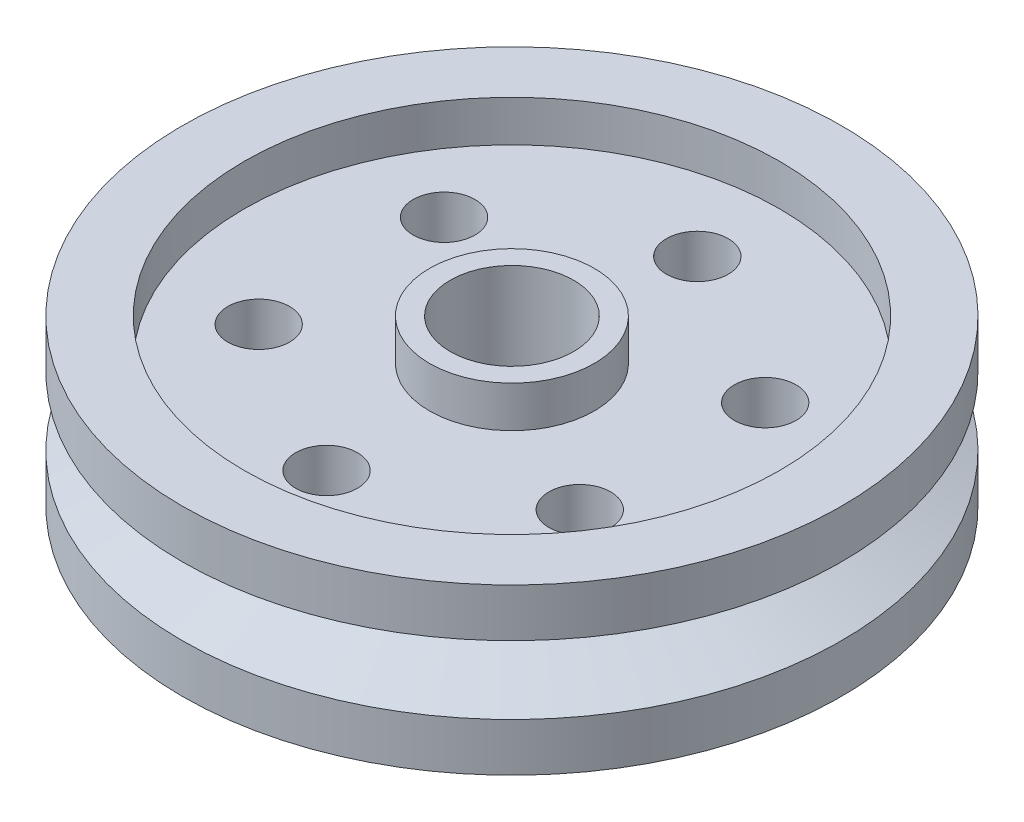
SolidWorks part; units mm, degrees
material "Aluminum Bronze"
ref_plane "Front" through (0, 0, 0) normal (0, 0, 1) x (1, 0, 0)
ref_plane "Top" through (0, 0, 0) normal (0, 1, 0) x (1, 0, 0)
ref_plane "Right" through (0, 0, 0) normal (1, 0, 0) x (0, 0, -1)
sketch "Sketch1" plane through (0, 0, 0) normal (0, 0, 1) x (1, 0, 0)
  line L0 (0, 218.8321) -> (0, -193.7631) construction
  line L1 (-236.0671, 0) -> (246.5126, 0) construction
  line L2 (0, 0) -> (0, 12.7)
  line L3 (0, 12.7) -> (50.8, 12.7)
  line L4 (50.8, 12.7) -> (50.8, 5.2605)
  line L5 (50.8, 5.2605) -> (38.1, 0)
  line L6 (38.1, 0) -> (0, 0)
  dimension "D1" = 101.6
  dimension "D2" = 12.7
  dimension "D3" = 22.5
  dimension "D4" = 25.4
revolve "Revolve1" add sketch "Sketch1" angle 360 about L0
sketch "Sketch2" plane through (0, 12.7, 0) normal (0, 1, 0) x (1, 0, 0)
  circle A0 centre (0, 0) radius 41.275
  circle A1 centre (0, 0) radius 12.7
  dimension "D1" = 82.55
  dimension "D2" = 25.4
extrude "Cut-Extrude1" cut sketch "Sketch2" against normal blind 6.35
sketch "Sketch3" plane through (0, 12.7, 0) normal (0, 1, 0) x (1, 0, 0)
  circle A0 centre (0, 0) radius 9.525
  dimension "D1" = 19.05
extrude "Cut-Extrude2" cut sketch "Sketch3" against normal through all
sketch "Sketch5" plane through (0, 6.35, 0) normal (0, 1, 0) x (1, 0, 0)
  circle A0 centre (0, 0) radius 28.575 construction
  circle A1 centre (0, 28.575) radius 4.7625
  dimension "D1" = 57.15
  dimension "D2" = 9.525
extrude "Cut-Extrude3" cut sketch "Sketch5" against normal through all
pattern_circular "CirPattern1" count 6 over 360 about axis through (0, 0, 0) along (0, 1, 0) of "Cut-Extrude3"
mirror "Mirror1" about plane through (0, 0, 0) normal (0, 1, 0) of bodies 105
